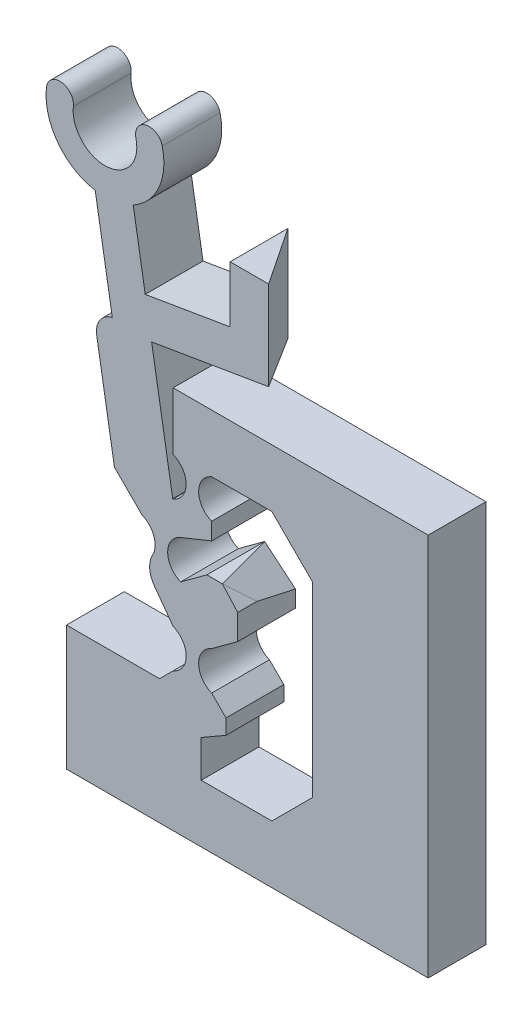
SolidWorks part; units mm, degrees
ref_plane "Front Plane" through (0, 0, 0) normal (0, 0, 1) x (1, 0, 0)
ref_plane "Top Plane" through (0, 0, 0) normal (0, 1, 0) x (1, 0, 0)
ref_plane "Right Plane" through (0, 0, 0) normal (1, 0, 0) x (0, 0, -1)
sketch "Sketch-SkeletonConfigUp" plane through (0, 0, 0) normal (0, 0, 1) x (1, 0, 0)
  line L0 (0, 0) -> (0, -50000) construction
  line L1 (0, 0) -> (4.5811, 6.2164) construction
  line L2 (9.8143, 13.3177) -> (4.5811, 13.945) construction
  line L3 (4.5811, 13.945) -> (2.9713, 10.4094) construction
  line L4 (2.9713, 10.4094) -> (4.5811, 6.2164) construction
  line L5 (4.5811, 13.945) -> (6.2429, 19.1409) construction
  line L6 (2.9713, 10.4094) -> (0.0405, 27.8193) construction
  line L7 (4.5811, 6.2164) -> (9.8143, 13.3177) construction
  line L8 (-587.3593, -797.0242) -> (9.8143, 13.3177) construction
  dimension "D2" = 7.7221
  dimension "D3" = 8.8212
  dimension "D4" = 5.2707
  dimension "D5" = 119.553
  dimension "D6" = 3.8848
  dimension "D7" = 5.4552
  dimension "D8" = 17.6549
  dimension "D9" = 4.4914
  dimension "D10" = 6.745
  dimension "D11" = 145.964
  dimension "D12" = 143.612
sketch "Sketch-SkeletonConfigDown" plane through (0, 0, 0) normal (0, 0, 1) x (1, 0, 0)
  line L0 (0, 0) -> (0, -50000) construction
  line L1 (0, 0) -> (4.5811, 6.2164) construction
  line L2 (9.8143, 13.3177) -> (4.5811, 13.945) construction
  line L3 (4.5811, 13.945) -> (6.1909, 10.4094) construction
  line L4 (6.1909, 10.4094) -> (4.5811, 6.2164) construction
  line L5 (4.5811, 13.945) -> (1.753, 18.6098) construction
  line L6 (6.1909, 10.4094) -> (-8.8652, 19.6294) construction
  line L7 (4.5811, 6.2164) -> (9.8143, 13.3177) construction
  line L8 (-589.9357, -800.5203) -> (9.8143, 13.3177) construction
  dimension "D2" = 7.7221
  dimension "D3" = 8.8212
  dimension "D4" = 5.2707
  dimension "D5" = 119.553
  dimension "D6" = 3.8848
  dimension "D7" = 5.4552
  dimension "D8" = 17.6549
  dimension "D9" = 4.4914
  dimension "D10" = 6.745
  dimension "D11" = 145.964
  dimension "D1" = 143.612
sketch "Sketch-SwitchBossUp" plane through (0, 0, 0) normal (0, 0, 1) x (1, 0, 0)
  line L0 (3.5811, 11.4759) -> (3.5811, 12.945) construction
  line L1 (5.5811, 11.1782) -> (5.5811, 12.0586) construction
  line L2 (6.5405, 22.165) -> (6.5405, 25.0939)
  line L3 (6.5405, 25.0939) -> (8.5405, 25.0939)
  line L4 (8.5405, 25.0939) -> (8.5405, 20.4736)
  line L5 (5.5811, 12.945) -> (5.5811, 12.0586)
  line L7 (1.507, 25.1315) -> (2.1313, 21.4228)
  line L8 (-0.4652, 24.7995) -> (0.4216, 19.5312)
  line L9 (2.9713, 10.4094) -> (0.0405, 27.8193) construction
  line L10 (2.6034, 8.5483) -> (3.5811, 7.2164)
  line L11 (-0.0396, 22.2712) -> (1.9326, 22.6032) construction
  line L15 (4.7006, 8.6678) -> (2.8518, 7.958) construction
  line L16 (2.9713, 10.4094) -> (4.5811, 6.2164) construction
  line L17 (3.5811, 12.945) -> (3.5811, 14.945) construction
  line L18 (5.5811, 12.945) -> (5.5811, 14.945) construction
  line L19 (4.2561, 13.945) -> (4.9061, 13.945) construction
  line L20 (3.5811, 14.945) -> (5.5811, 14.945) construction
  line L21 (3.5811, 12.945) -> (5.5811, 12.945) construction
  line L22 (4.5811, 12.945) -> (4.5811, 14.945) construction
  line L23 (4.5811, 6.2164) -> (8.5405, 7.1023) construction
  line L24 (1.9713, 9.4094) -> (1.9713, 11.4094) construction
  line L25 (3.9713, 9.4094) -> (3.9713, 11.4094) construction
  line L26 (3.9713, 9.4094) -> (1.9713, 9.4094) construction
  line L27 (1.9713, 11.4094) -> (3.9713, 11.4094) construction
  line L28 (3.5811, 7.2164) -> (5.5811, 7.2164) construction
  line L29 (3.5811, 7.2164) -> (3.5811, 5.2164) construction
  line L30 (5.5811, 7.2164) -> (5.5811, 5.2164) construction
  line L31 (3.5811, 5.2164) -> (5.5811, 5.2164) construction
  line L32 (4.9061, 6.2164) -> (4.2561, 6.2164) construction
  line L40 (3.2963, 10.4094) -> (2.6463, 10.4094) construction
  line L43 (2.874, 4.5093) -> (-1.9548, 4.5093)
  line L44 (-1.9548, 4.5093) -> (-1.9548, -1.9756)
  line L45 (-1.9548, -1.9756) -> (5.0405, -1.9756)
  line L46 (5.0405, 1.0244) -> (5.0405, 2.9474)
  line L51 (6.5405, 22.165) -> (2.1313, 21.4228)
  line L61 (6.8113, 14.945) -> (6.8113, 17.945) construction
  line L66 (0.0405, 27.8193) -> (0.0405, 50027.8193) construction
  line L74 (0.5326, 12.848) -> (-0.3888, 18.3216)
  line L75 (0.3841, 13.7302) -> (2.3564, 14.0622) construction
  line L76 (5.5811, 12.0586) -> (5.5811, 12.945) construction
  line L77 (6.7548, 8.2037) -> (5.0019, 8.2037) construction
  line L80 (6.1339, 10.409) -> (6.9354, 9.5189)
  line L81 (8.5405, 7.9632) -> (8.5405, -49992.0368) construction
  line L82 (2.1313, 21.4228) -> (3.5585, 12.945) construction
  line L83 (3.5585, 12.945) -> (2.4634, 19.4505)
  line L84 (2.4634, 19.4505) -> (8.5405, 20.4736)
  line L85 (6.9307, 9.5241) -> (8.5405, 7.7363) construction
  line L86 (5.5811, 7.2164) -> (6.9354, 8.2106)
  line L88 (3.5811, 17.945) -> (6.8113, 17.945)
  line L92 (3.7762, 8.3129) -> (6.9307, 9.5241) construction
  line L93 (6.3271, 3.6903) -> (5.0405, 2.9474)
  line L94 (3.5811, 14.945) -> (3.5811, 17.945)
  line L95 (2.1313, 21.4228) -> (2.4634, 19.4505) construction
  line L96 (2.2974, 20.4367) -> (8.5405, 21.4876) construction
  line L97 (2.2974, 20.4367) -> (1.3112, 20.2707) construction
  line L98 (6.7548, 8.2037) -> (4.7691, 10.409) construction
  line L99 (4.5811, 6.2164) -> (6.1339, 10.409) construction
  line L100 (4.5811, 6.2164) -> (8.5405, 8.2931) construction
  line L101 (4.5811, 6.2164) -> (6.9307, 9.5241) construction
  line L102 (3.5585, 12.945) -> (3.5811, 12.945)
  line L103 (8.5405, 20.4736) -> (8.5405, 8.2931) construction
  line L104 (6.9307, 9.5241) -> (8.5405, 7.7363) construction
  line L106 (6.8113, 14.945) -> (5.5811, 14.945)
  line L107 (1.9713, 9.4094) -> (2.6034, 8.5483) construction
  line L109 (7.3693, 7.7363) -> (8.5405, 7.7363) construction
  line L110 (8.5405, 7.7363) -> (7.3693, 7.7363) construction
  line L111 (6.9354, 9.5189) -> (6.9354, 8.2106)
  line L112 (6.9354, 9.5189) -> (6.9307, 9.5241) construction
  line L114 (7.3693, 7.7363) -> (7.3563, 7.7363) construction
  line L115 (6.8113, 17.945) -> (16.8281, 17.945)
  line L116 (16.8281, 17.945) -> (16.8281, -1.9756)
  line L117 (16.8281, -1.9756) -> (5.0405, -1.9756)
  line L118 (6.8113, 14.945) -> (8.7068, 14.945)
  line L119 (10.8281, 12.8236) -> (10.8281, 3.1457)
  line L120 (8.7068, 1.0244) -> (5.0405, 1.0244)
  line L121 (5.0405, -1.9756) -> (5.0405, 1.0244) construction
  line L122 (10.8281, 14.945) -> (13.8281, 14.945) construction
  line L123 (13.8281, 14.945) -> (16.8281, 14.945) construction
  line L124 (10.8281, 3.1457) -> (8.7068, 1.0244)
  line L125 (10.8281, 7.9847) -> (16.8281, 7.9847) construction
  line L126 (10.8281, 12.8236) -> (8.7068, 14.945)
  line L127 (8.5405, 14.945) -> (10.8281, 14.945) construction
  line L128 (10.8281, 14.945) -> (10.8281, 12.8236) construction
  line L129 (10.8281, 3.1457) -> (10.8281, 1.0244) construction
  line L130 (10.8281, 1.0244) -> (8.7068, 1.0244) construction
  line L133 (2.9713, 10.4094) -> (6.1909, 10.4094) construction
  line L134 (4.5811, 10.4094) -> (4.5811, 13.945) construction
  line L135 (4.5811, 10.4094) -> (4.5811, 6.2164) construction
  line L136 (1.9713, 11.4094) -> (0.5326, 12.848)
  line L137 (3.9713, 9.4094) -> (5.5811, 7.2164) construction
  line L138 (3.5811, 5.2164) -> (2.874, 4.5093)
  line L139 (5.333, 10.409) -> (3.9713, 9.4094)
  line L143 (4.7691, 10.409) -> (5.333, 10.409) construction
  line L144 (5.333, 10.409) -> (6.1339, 10.409)
  line L145 (4.5811, 10.4534) -> (4.7691, 10.409) construction
  line L146 (3.9713, 11.4094) -> (5.5811, 12.0586)
  line L147 (5.5811, 12.0586) -> (5.5811, 12.945) construction
  line L148 (5.5811, 5.2164) -> (6.3271, 4.4705)
  line L149 (6.3271, 4.4705) -> (6.3271, 3.6903)
  arc A0 (1.507, 25.1315) -> (3.0168, 28.5383) centre (0.0405, 27.8193) ccw
  arc A1 (-0.4652, 24.7995) -> (-3.0011, 28.1713) centre (0.0405, 27.8193) cw
  arc A2 (-3.0011, 28.1713) -> (-1.6023, 28.0095) centre (-2.3017, 28.0904) cw
  arc A3 (3.0168, 28.5383) -> (1.648, 28.2077) centre (2.3324, 28.373) ccw
  arc A4 (-1.6023, 28.0095) -> (1.648, 28.2077) centre (0.0405, 27.8193) ccw
  arc A5 (3.5811, 12.945) -> (3.5811, 14.945) centre (3.1778, 13.945) ccw
  arc A6 (5.5811, 12.945) -> (5.5811, 14.945) centre (5.9843, 13.945) cw
  arc A7 (2.5141, 9.892) -> (1.9713, 11.4094) centre (1.568, 10.4094) ccw
  arc A8 (3.9713, 11.4094) -> (3.9713, 9.4094) centre (4.3745, 10.4094) ccw
  arc A9 (3.5811, 7.2164) -> (3.5811, 5.2164) centre (3.1779, 6.2164) cw
  arc A10 (5.5811, 7.2164) -> (5.5811, 5.2164) centre (5.9844, 6.2164) ccw
  arc A19 (-0.3888, 18.3216) -> (0.4216, 19.5312) centre (0.6565, 18.4975) cw
  arc A27 (2.5141, 9.892) -> (2.6034, 8.5483) centre (3.6143, 9.2904) ccw
  arc A28 (6.21, 3.6227) -> (5.2269, 3.6539) centre (5.7492, 4.6041) cw construction
  arc A29 (1.9713, 9.4094) -> (2.5141, 9.892) centre (1.568, 10.4094) ccw construction
  point P35 (0, 0)
  point P44 (3.7762, 8.3129)
  point P53 (4.5811, 13.945)
  point P63 (2.9713, 10.4094)
  point P93 (0.9465, 22.4372)
  dimension "D1" = 2
  dimension "D2" = 2
  dimension "D3" = 2
  dimension "D4" = 3
  dimension "D5" = 2
  dimension "D6" = 0.65
  dimension "D7" = 2
  dimension "D8" = 42
  dimension "D9" = 3
  dimension "D10" = 5
  dimension "D11" = 8.5
  dimension "D12" = 120
  dimension "D14" = 10
  dimension "D15" = 45
  dimension "D16" = 42
  dimension "D18" = 3
  dimension "D19" = 135
  dimension "D20" = 135
  dimension "D21" = 1
  dimension "D22" = 135
extrude "Boss-SwitchMain" add sketch "Sketch-SwitchBossUp" along normal blind 3
sketch "Sketch1" plane through (0, 0, 0) normal (0, 0, -1) x (-1, 0, 0)
  line L0 (1.9548, 4.5093) -> (1.9548, -1.9756) construction
  line L1 (-4.628, -1.1895) -> (1.9548, -1.1895)
  line L2 (-4.628, -1.1895) -> (-4.628, 0.3105)
  line L3 (-4.628, 0.3105) -> (1.9548, 0.3105)
  line L4 (1.9548, -1.1895) -> (1.9548, 0.3105)
  line L5 (-3.5811, 17.945) -> (-6.6395, 17.945)
  line L6 (-2.5363, 4.5093) -> (1.9548, 4.5093)
  line L7 (-2.5363, 4.5093) -> (-2.5363, 3.0093)
  line L8 (-2.5363, 3.0093) -> (1.9548, 3.0093)
  line L9 (1.9548, 4.5093) -> (1.9548, 3.0093)
  line L10 (-6.6395, 17.945) -> (-6.8113, 16.4548)
  line L11 (-2.874, 4.5093) -> (1.9548, 4.5093) construction
  line L12 (-6.8113, 16.4548) -> (-3.5811, 16.4548)
  line L13 (-5.128, -1.3839) -> (-5.128, 7.6731) construction
  line L14 (-3.5811, 16.4548) -> (-3.5811, 17.945)
  line L18 (-3.5811, 17.945) -> (-3.5811, 14.945) construction
  line L19 (-5.128, -1.3839) -> (-5.128, 7.6731) construction
  line L20 (-6.8113, 17.945) -> (-16.8281, 17.945) construction
  line L21 (-6.8113, 14.945) -> (-6.8113, 17.945) construction
  dimension "D1" = 1.5
  dimension "D2" = 1.5
  dimension "D3" = 1.5
  dimension "D4" = 0.5
extrude "Boss-Flange Width" add sketch "Sketch1" along normal blind 6
ref_plane "Plane-Sta2Sit Groove" through (0.0405, 0, 0) normal (1, 0, 0) x (0, 0, -1)
ref_plane "Plane-Cam Face" through (-12.0395, 0, 0) normal (1, 0, 0) x (0, 0, -1)
ref_plane "Plane-FlangeTop" through (-7.0395, 0, 0) normal (1, 0, 0) x (0, 0, -1)
sketch "Sketch2" plane through (-7.0395, 0, 0) normal (1, 0, 0) x (0, 0, -1)
  line L0 (6, 16.4548) -> (0, 16.4548) construction
  line L1 (6, 17.945) -> (1, 17.945)
  line L2 (6, 17.945) -> (6, 16.4548)
  line L3 (6, 16.4548) -> (1, 16.4548)
  line L4 (1, 17.945) -> (1, 16.4548)
  line L5 (6, 3.0093) -> (0, 3.0093) construction
  line L6 (6, 4.5093) -> (1, 4.5093)
  line L7 (6, 4.5093) -> (6, 3.0093)
  line L8 (6, 3.0093) -> (1, 3.0093)
  line L9 (1, 4.5093) -> (1, 3.0093)
  line L10 (-3, -1.9756) -> (0, -1.9756) construction
  line L11 (6, 0.3105) -> (1, 0.3105)
  line L12 (6, 0.3105) -> (6, -1.9756)
  line L13 (6, -1.9756) -> (1, -1.9756)
  line L14 (1, 0.3105) -> (1, -1.9756)
  line L15 (0, 10.4094) -> (0, 27.8193) construction
  dimension "D1" = 1
extrude "Boss-Flange Height" add sketch "Sketch2" along normal up to surface (11.6675 mm away)
sketch "Sketch-HolePositions" plane through (0, -1.9756, 0) normal (0, -1, 0) x (1, 0, 0)
  line L0 (-7.0395, -3.5) -> (4.628, -3.5) construction
  line L2 (4.628, -1) -> (4.628, 0) construction
  line L3 (4.628, -1) -> (-7.0395, -1) construction
  line L4 (-7.0395, -22.2167) -> (-7.0395, 22.2167) construction
  point P6 (-4.0395, -3.5)
  point P7 (1.628, -3.5)
  dimension "D1" = 3
  dimension "D2" = 3
  dimension "D3" = 2.5
sketch "Sketch6" plane through (0, -1.9756, 0) normal (0, -1, 0) x (-1, 0, 0)
  point P0 (4.0395, 3.5)
  point P3 (-1.628, 3.5)
hole_wizard "Tap Drill for M2x0.4 Tap1" positions "Sketch6" profile "Sketch5" hole size "M2x0.4" standard "ANSI Metric" end condition through all
sketch "Sketch5" plane through (-4.0395, -1.9756, -3.5) normal (1, 0, 0) x (0, 0, -1)
  line L0 (0, 0) -> (0, 31.0527)
  line L1 (0, 31.0527) -> (0.8, 31.0527)
  line L2 (0.8, 31.0527) -> (0.8, 0)
  line L5 (0.8, 0) -> (0, 0)
  line L11 (0, -6.35) -> (0, 107.95) construction
  dimension "Thru Hole Dia." = 1.6
  dimension "Thru Hole Depth" = 31.0527
sketch "Sketch9" plane through (0, -1.9756, 0) normal (0, -1, 0) x (1, 0, 0)
  point P0 (-4.0395, -3.5)
  point P3 (1.628, -3.5)
hole_wizard "M2 Clearance Hole2" positions "Sketch9" profile "Sketch8" hole size "M2" standard "ANSI Metric"
sketch "Sketch8" plane through (-4.0395, -1.9756, -3.5) normal (1, 0, 0) x (0, 0, -1)
  line L0 (0, 0) -> (0, 7.206)
  line L1 (0, 7.206) -> (1.2, 6.4849)
  line L2 (1.2, 6.4849) -> (1.2, 0)
  line L5 (1.2, 0) -> (0, 0)
  line L10 (0, 7.206) -> (-1.2, 6.4849) construction
  line L11 (0, -6.35) -> (0, 107.95) construction
  dimension "Hole Dia." = 2.4
  dimension "Hole Depth" = 6.4849
  dimension "Drill Angle" = 118
sketch "Sketch10" plane through (0, 17.945, 0) normal (0, 1, 0) x (1, 0, 0)
  line L1 (6.6395, 6) -> (5.128, 6)
  line L2 (6.6395, 6) -> (6.6395, 3)
  line L3 (6.6395, 3) -> (5.128, 3)
  line L5 (4.628, 7) -> (4.628, 1) construction
  line L6 (3.5811, 1) -> (-7.0395, 1) construction
  line L7 (5.128, 6.25) -> (5.128, 1) construction
  line L8 (5.128, 6) -> (5.128, 3)
  dimension "D1" = 2
extrude "Cut-Flange Ramp Clearance" cut sketch "Sketch10" against normal up to next
sketch "Sketch-Measurements for Derailleur Ramps" plane through (0, 0, 0) normal (0, 0, 1) x (1, 0, 0)
  line L0 (2.4634, 19.4505) -> (2.1313, 21.4228)
  line L1 (2.2974, 20.4367) -> (1.3112, 20.2707)
  line L2 (2.9713, 10.4094) -> (0.0405, 27.8193) construction
  line L3 (1.3112, 20.2707) -> (-4.0257, 16.6658)
  line L4 (6.1909, 10.4094) -> (-8.8652, 19.6294) construction
  line L5 (1.3112, 20.2707) -> (2.6012, 12.6077)
  line L6 (2.6012, 12.6077) -> (-4.0257, 16.6658)
  line L7 (-1.3573, 18.4682) -> (-1.3573, 20.2707)
  line L8 (-1.3573, 20.2707) -> (1.3112, 20.2707)
  line L9 (6.1909, 10.4094) -> (2.9713, 10.4094)
  line L10 (5.386, 8.3129) -> (3.7762, 8.3129)
  line L12 (6.1909, 10.4094) -> (4.5811, 6.2164) construction
  line L13 (4.5811, 8.3129) -> (4.5811, 8.7912)
  line L14 (4.5811, 6.2164) -> (5.386, 8.3129)
  line L15 (2.9713, 10.4094) -> (4.5811, 6.2164) construction
  line L16 (3.7762, 8.3129) -> (4.5811, 6.2164)
  line L17 (5.386, 8.3129) -> (5.386, 8.7912)
  dimension "D1" = 2.6685
  dimension "D2" = 0.8049
sketch "Sketch12" plane through (0, 25.0939, 0) normal (0, 1, 0) x (1, 0, 0)
  line L0 (6.5405, 0) -> (8.5405, -3)
  line L1 (8.5405, -3) -> (8.5405, 0)
  line L2 (8.5405, 0) -> (6.5405, 0)
extrude "Cut-Extrude1" cut sketch "Sketch12" against normal up to next
ref_plane "Plane1" through (0, 7.1023, 0) normal (0, 1, 0) x (1, 0, 0)
sketch "Sketch-Derailleur Location" plane through (0, 7.1023, 0) normal (0, 1, 0) x (1, 0, 0)
  line L0 (8.5405, 0) -> (8.5405, -3)
  line L1 (3.5811, -3) -> (4.2561, -3) construction
  line L2 (-119237.4187, 0) -> (9.8143, 0) construction
  point P0 (8.5405, 0)
  point P8 (8.5405, -1.5)
ref_plane "Plane-Cantilever Cut" through (7.0973, 8.5173, -1.8949) normal (-0.631, -0.7573, 0.1685) x (-0.7758, 0.616, -0.137)
sketch "Sketch14" plane through (7.0973, 8.5173, -1.8949) normal (-0.631, -0.7573, 0.1685) x (-0.7758, 0.616, -0.137)
  line L0 (2.5653, -1.6911) -> (-0.4368, -1.6911)
  line L2 (2.5653, -5.3731) -> (2.5653, -1.6911)
  line L3 (-0.4368, -1.6911) -> (-0.4368, -5.3731)
  line L4 (-0.4368, -5.3731) -> (2.5653, -5.3731)
extrude "Cut-Extrude2" cut sketch "Sketch14" against normal up to next
sketch "Sketch15" plane through (0, 0, 0) normal (0, 0, -1) x (-1, 0, 0)
  line L1 (-10.0534, 18.2157) -> (8.3706, 18.2157)
  line L2 (-10.0534, 18.2157) -> (-10.0534, -2.1599)
  line L3 (-10.0534, -2.1599) -> (8.3706, -2.1599)
  line L4 (8.3706, 18.2157) -> (8.3706, -2.1599)
extrude "Cut-Extrude3" cut sketch "Sketch15" along normal through all
equation "\"axle-diameter\"=2"
equation "\"switch-thickness\"=12"
equation "\"base-width\"=4.0"
equation "\"axle-bushing-radius\"=3"
equation "\"clearance\"= 0.25"
equation "\"arm-width\"=1.5"
equation "\"min-diameter\"=70"
equation "\"alpha\"=143.6120"
equation "\"gamma\"=119.5526"
equation "\"delta\"=145.9637"
equation "\"epsilon\"=6.7452"
equation "\"l_AB\"=8.8212"
equation "\"l_AC\"=4.4914"
equation "\"l_BD\"=5.2707"
equation "\"l_CD\"=3.8848"
equation "\"l_CE\"=17.6549"
equation "\"l_DF\"=5.4552"
equation "\"l_OA\"=7.7221"
equation "\"D2@Sketch-SkeletonConfigUp\" = \"l_OA\""
equation "\"D3@Sketch-SkeletonConfigUp\" = \"l_AB\""
equation "\"D4@Sketch-SkeletonConfigUp\" = \"l_BD\""
equation "\"D5@Sketch-SkeletonConfigUp\" = \"gamma\""
equation "\"D6@Sketch-SkeletonConfigUp\" = \"l_CD\""
equation "\"D7@Sketch-SkeletonConfigUp\" = \"l_DF\""
equation "\"D8@Sketch-SkeletonConfigUp\" = \"l_CE\""
equation "\"D9@Sketch-SkeletonConfigUp\" = \"l_AC\""
equation "\"D_groove\"=3.175"
equation "\"D7@Sketch-SkeletonConfigDown\" = \"l_DF\""
equation "\"D6@Sketch-SkeletonConfigDown\" = \"l_CD\""
equation "\"D2@Sketch-SkeletonConfigDown\" = \"l_OA\""
equation "\"D3@Sketch-SkeletonConfigDown\" = \"l_AB\""
equation "\"D9@Sketch-SkeletonConfigDown\" = \"l_AC\""
equation "\"D8@Sketch-SkeletonConfigDown\" = \"l_CE\""
equation "\"D5@Sketch-SkeletonConfigDown\" = \"gamma\""
equation "\"D4@Sketch-SkeletonConfigDown\" = \"l_BD\""
equation "\"D1@Sketch-SkeletonConfigDown\" = \"alpha\""
equation "\"hinge_length\"=1.5"
equation "\"hinge_depth\"=0.25"
equation "\"D10@Sketch-SkeletonConfigUp\"=\"epsilon\""
equation "\"D11@Sketch-SkeletonConfigUp\"=\"delta\""
equation "\"D12@Sketch-SkeletonConfigUp\"=\"alpha\""
equation "\"D11@Sketch-SkeletonConfigDown\"=\"delta\""
equation "\"D10@Sketch-SkeletonConfigDown\"=\"epsilon\""
equation "\"EE_dx\"=8.9056"
equation "\"EE_dy\"=8.1898"
equation "\"r_groove\"=\"D_groove\"/2"
equation "\"t_wall\"=25.4/16"
equation "\"width_lower\"=\"D_groove\"+\"t_wall\""
equation "\"cable_to_bottom\"=30.6257"
equation "\"switch_EE-up_base_dy\"=24"
equation "\"switch_EE-down_base_dy\"=16"
equation "\"D_axle\"=25.4/8"
equation "\"D_up_to_down\"=16"
equation "\"D_down_to_up\"=25"
equation "\"t_cam_base\"=7.5"
